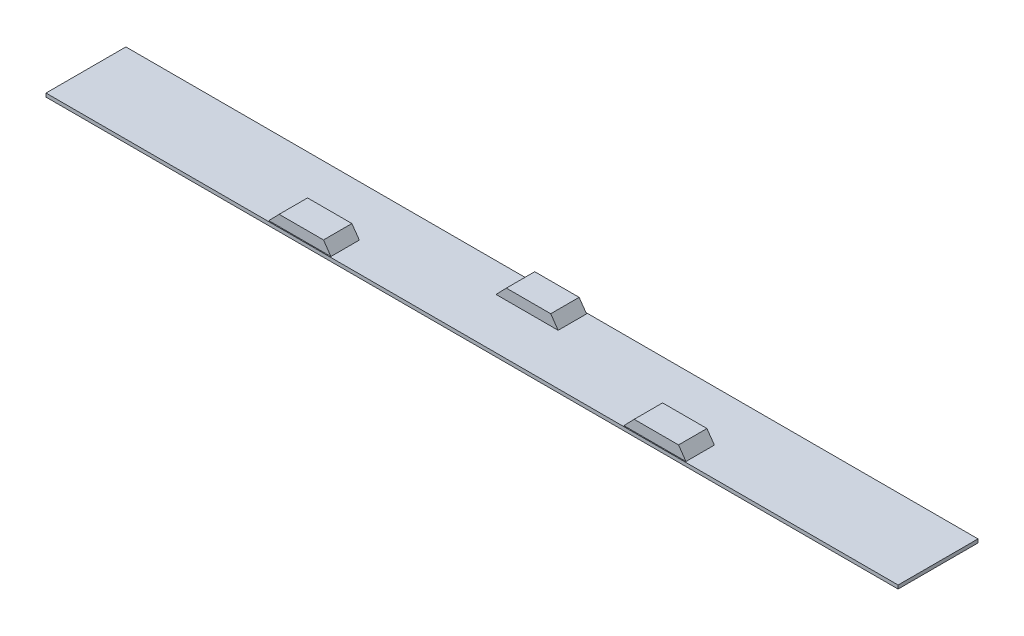
SolidWorks part; units mm, degrees
ref_plane "Front Plane" through (0, 0, 0) normal (0, 0, 1) x (1, 0, 0)
ref_plane "Top Plane" through (0, 0, 0) normal (0, 1, 0) x (1, 0, 0)
ref_plane "Right Plane" through (0, 0, 0) normal (1, 0, 0) x (0, 0, -1)
sketch "Sketch1" plane through (0, 0, 0) normal (0, 1, 0) x (1, 0, 0)
  line L1 (1200, 112.5) -> (-1200, 112.5)
  line L2 (1200, 112.5) -> (1200, -112.5)
  line L3 (1200, -112.5) -> (-1200, -112.5)
  line L4 (-1200, 112.5) -> (-1200, -112.5)
  line L5 (1200, 112.5) -> (-1200, -112.5) construction
  line L6 (1200, -112.5) -> (-1200, 112.5) construction
  point P0 (0, 0)
  dimension "D1" = 2400
  dimension "D2" = 225
extrude "Boss-Extrude1" add sketch "Sketch1" along normal blind 10
sketch "Sketch2" plane through (0, 0, 0) normal (0, 0, 1) x (1, 0, 0)
  line L0 (600, 10) -> (579.0927, 40)
  line L1 (-1200, 10) -> (1200, 10) construction
  line L2 (579.0927, 40) -> (454.0927, 40)
  line L3 (454.0927, 40) -> (425, 10)
  line L4 (425, 10) -> (600, 10)
  line L5 (1200, 10) -> (1200, 0) construction
  line L6 (-420.9073, 40) -> (-545.9073, 40)
  line L7 (-545.9073, 40) -> (-575, 10)
  line L8 (-400, 10) -> (-420.9073, 40)
  line L9 (-575, 10) -> (-400, 10)
  line L10 (579.0927, 40) -> (-420.9073, 40) construction
  dimension "D1" = 125
  dimension "D2" = 30
  dimension "D3" = 175
  dimension "D4" = 600
  dimension "D5" = 2
  dimension "D6" = 1000
extrude "Boss-Extrude2" add sketch "Sketch2" along normal blind 80 from offset 30
sketch "Sketch4" plane through (0, 0, 0) normal (0, 0, 1) x (1, 0, 0)
  line L0 (100, 10) -> (79.0927, 40)
  line L1 (79.0927, 40) -> (-45.9073, 40)
  line L2 (-45.9073, 40) -> (-75, 10)
  line L3 (-75, 10) -> (100, 10)
  line L4 (600, 10) -> (579.0927, 40)
  line L5 (579.0927, 40) -> (454.0927, 40)
  line L6 (454.0927, 40) -> (425, 10)
  line L7 (425, 10) -> (600, 10)
  line L8 (600, 10) -> (579.0927, 40)
  line L9 (579.0927, 40) -> (454.0927, 40)
  line L10 (454.0927, 40) -> (425, 10)
  line L11 (425, 10) -> (600, 10)
  line L12 (600, 10) -> (100, 10) construction
  dimension "D3" = 500
  dimension "D1" = 0
  dimension "D2" = 2
extrude "Boss-Extrude3" add sketch "Sketch4" against normal blind 80 from offset 30 contours L0 L1 L2 L3
